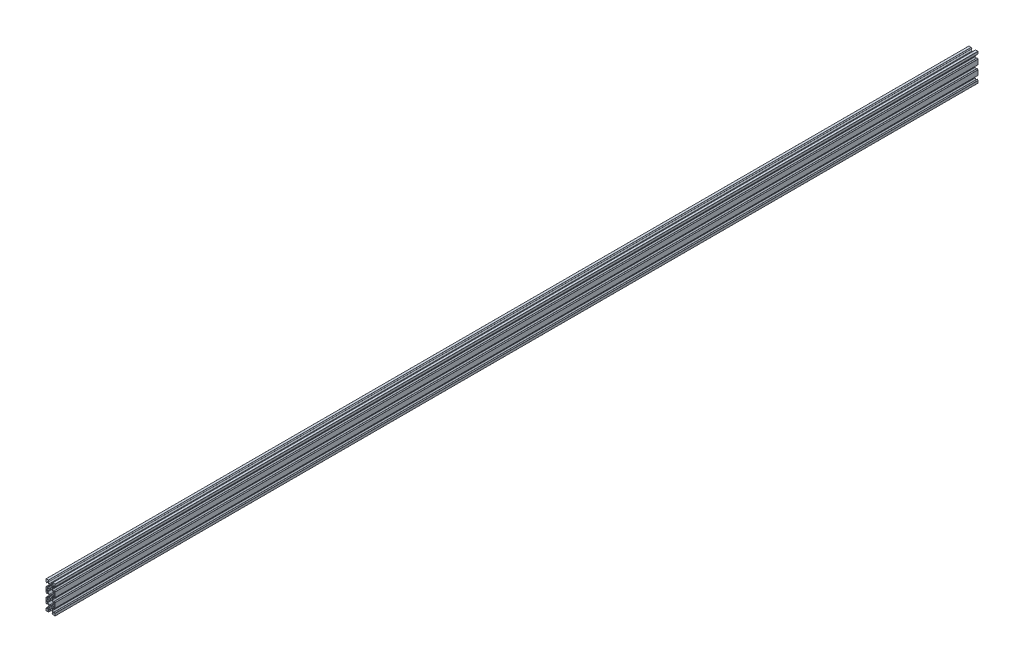
SolidWorks part; units mm, degrees
material "6063-T5"
ref_plane "Plan de face" through (0, 0, 0) normal (0, 0, 1) x (1, 0, 0)
ref_plane "Plan de dessus" through (0, 0, 0) normal (0, 1, 0) x (1, 0, 0)
ref_plane "Plan de droite" through (0, 0, 0) normal (1, 0, 0) x (0, 0, -1)
sketch "Esquisse1" plane through (0, 0, 0) normal (0, 0, 1) x (1, 0, 0)
  line L12 (10.4135, -7.6873) -> (8.8378, -7.6873)
  line L13 (8.6256, -7.5995) -> (5.4414, -4.4152)
  line L14 (5.2292, -4.3273) -> (3.0331, -4.3273)
  line L15 (3.0331, -4.3273) -> (2.5135, -4.0273)
  line L16 (2.5135, -4.0273) -> (1.9939, -4.3273)
  line L17 (1.9939, -4.3273) -> (-0.2022, -4.3273)
  line L18 (-0.4144, -4.4152) -> (-3.5986, -7.5995)
  line L19 (-3.8108, -7.6873) -> (-5.3865, -7.6873)
  line L20 (-5.6865, -7.9873) -> (-5.6865, -10.4267)
  line L21 (-5.6865, -10.4267) -> (-5.6865, -12.866)
  line L22 (-5.3865, -13.166) -> (-3.8108, -13.166)
  line L23 (-3.5986, -13.2539) -> (-0.4144, -16.4382)
  line L24 (-0.2022, -16.526) -> (1.9939, -16.526)
  line L25 (1.9939, -16.526) -> (2.5135, -16.826)
  line L26 (2.5135, -16.826) -> (3.0331, -16.526)
  line L27 (3.0331, -16.526) -> (5.2292, -16.526)
  line L28 (5.4414, -16.4382) -> (8.6256, -13.2539)
  line L29 (8.8378, -13.166) -> (10.4135, -13.166)
  line L30 (10.7135, -12.866) -> (10.7135, -10.4267)
  line L31 (10.7135, -10.4267) -> (10.7135, -7.9873)
  line L38 (10.4135, 12.3127) -> (8.8378, 12.3127)
  line L39 (8.6256, 12.4005) -> (5.4414, 15.5848)
  line L40 (5.2292, 15.6727) -> (3.0331, 15.6727)
  line L41 (3.0331, 15.6727) -> (2.5135, 15.9727)
  line L42 (2.5135, 15.9727) -> (1.9939, 15.6727)
  line L43 (1.9939, 15.6727) -> (-0.2022, 15.6727)
  line L44 (-0.4144, 15.5848) -> (-3.5986, 12.4005)
  line L45 (-3.8108, 12.3127) -> (-5.3865, 12.3127)
  line L46 (-5.6865, 12.0127) -> (-5.6865, 9.5733)
  line L47 (-5.6865, 9.5733) -> (-5.6865, 7.134)
  line L48 (-5.3865, 6.834) -> (-3.8108, 6.834)
  line L49 (-3.5986, 6.7461) -> (-0.4144, 3.5618)
  line L50 (-0.2022, 3.474) -> (1.9939, 3.474)
  line L51 (1.9939, 3.474) -> (2.5135, 3.174)
  line L52 (2.5135, 3.174) -> (3.0331, 3.474)
  line L53 (3.0331, 3.474) -> (5.2292, 3.474)
  line L54 (5.4414, 3.5618) -> (8.6256, 6.7461)
  line L55 (8.8378, 6.834) -> (10.4135, 6.834)
  line L56 (10.7135, 7.134) -> (10.7135, 9.5733)
  line L57 (10.7135, 9.5733) -> (10.7135, 12.0127)
  line L64 (6.1142, 19.5733) -> (6.4142, 20.0929)
  line L65 (6.4142, 20.0929) -> (6.4142, 22.2891)
  line L66 (6.502, 22.5012) -> (8.9856, 24.9848)
  line L67 (9.1978, 25.0727) -> (10.4135, 25.0727)
  line L68 (10.7135, 24.7727) -> (10.7135, 22.7733)
  line L69 (10.8842, 22.7026) -> (12.4256, 24.244)
  line L70 (12.5135, 24.4562) -> (12.5135, 29.2733)
  line L71 (12.2135, 29.5733) -> (7.3963, 29.5733)
  line L72 (7.1842, 29.4855) -> (5.6428, 27.944)
  line L73 (5.7135, 27.7733) -> (7.7128, 27.7733)
  line L74 (8.0128, 27.4733) -> (8.0128, 26.2576)
  line L75 (7.925, 26.0455) -> (5.4414, 23.5618)
  line L78 (5.2292, 23.474) -> (3.0331, 23.474)
  line L79 (3.0331, 23.474) -> (2.5135, 23.174)
  line L80 (2.5135, 23.174) -> (1.9939, 23.474)
  line L81 (1.9939, 23.474) -> (-0.2022, 23.474)
  line L84 (-0.4144, 23.5618) -> (-2.898, 26.0455)
  line L85 (-2.9858, 26.2576) -> (-2.9858, 27.4733)
  line L86 (-2.6858, 27.7733) -> (-0.6865, 27.7733)
  line L87 (-0.6158, 27.944) -> (-2.1572, 29.4855)
  line L88 (-2.3693, 29.5733) -> (-7.1865, 29.5733)
  line L89 (-7.4865, 29.2733) -> (-7.4865, 24.4562)
  line L90 (-7.3986, 24.244) -> (-5.8572, 22.7026)
  line L91 (-5.6865, 22.7733) -> (-5.6865, 24.7727)
  line L92 (-5.3865, 25.0727) -> (-4.1708, 25.0727)
  line L95 (-3.9586, 24.9848) -> (-1.475, 22.5012)
  line L96 (-1.3872, 22.2891) -> (-1.3872, 20.0929)
  line L97 (-1.3872, 20.0929) -> (-1.0872, 19.5733)
  line L98 (-1.0872, 19.5733) -> (-1.3872, 19.0537)
  line L99 (-1.3872, 19.0537) -> (-1.3872, 16.8576)
  line L100 (-1.475, 16.6455) -> (-3.9586, 14.1618)
  line L101 (-4.1708, 14.074) -> (-5.3865, 14.074)
  line L102 (-5.6865, 14.374) -> (-5.6865, 16.3733)
  line L103 (-5.8572, 16.444) -> (-7.3986, 14.9026)
  line L104 (-7.4865, 14.6905) -> (-7.4865, 9.5733)
  line L105 (-7.4865, 9.5733) -> (-7.4865, 4.4562)
  line L106 (-7.3986, 4.244) -> (-5.8572, 2.7026)
  line L107 (-5.6865, 2.7733) -> (-5.6865, 4.7727)
  line L108 (-5.3865, 5.0727) -> (-4.1708, 5.0727)
  line L109 (-3.9586, 4.9848) -> (-1.475, 2.5012)
  line L110 (-1.3872, 2.2891) -> (-1.3872, 0.0929)
  line L111 (-1.3872, 0.0929) -> (-1.0872, -0.4267)
  line L112 (-1.0872, -0.4267) -> (-1.3872, -0.9463)
  line L113 (-1.3872, -0.9463) -> (-1.3872, -3.1424)
  line L114 (-1.475, -3.3545) -> (-3.9586, -5.8382)
  line L115 (-4.1708, -5.926) -> (-5.3865, -5.926)
  line L116 (-5.6865, -5.626) -> (-5.6865, -3.6267)
  line L117 (-5.8572, -3.556) -> (-7.3986, -5.0974)
  line L118 (-7.4865, -5.3095) -> (-7.4865, -10.4267)
  line L119 (-7.4865, -10.4267) -> (-7.4865, -15.5438)
  line L120 (-7.3986, -15.756) -> (-5.8572, -17.2974)
  line L121 (-5.6865, -17.2267) -> (-5.6865, -15.2273)
  line L122 (-5.3865, -14.9273) -> (-4.1708, -14.9273)
  line L123 (-3.9586, -15.0152) -> (-1.475, -17.4988)
  line L124 (-1.3872, -17.7109) -> (-1.3872, -19.9071)
  line L125 (-1.3872, -19.9071) -> (-1.0872, -20.4267)
  line L126 (-1.0872, -20.4267) -> (-1.3872, -20.9463)
  line L127 (-1.3872, -20.9463) -> (-1.3872, -23.1424)
  line L128 (-1.475, -23.3545) -> (-3.9586, -25.8382)
  line L131 (-4.1708, -25.926) -> (-5.3865, -25.926)
  line L132 (-5.6865, -25.626) -> (-5.6865, -23.6267)
  line L133 (-5.8572, -23.556) -> (-7.3986, -25.0974)
  line L134 (-7.4865, -25.3095) -> (-7.4865, -30.1267)
  line L135 (-7.1865, -30.4267) -> (-2.3693, -30.4267)
  line L136 (-2.1572, -30.3388) -> (-0.6158, -28.7974)
  line L137 (-0.6865, -28.6267) -> (-2.6858, -28.6267)
  line L138 (-2.9858, -28.3267) -> (-2.9858, -27.1109)
  line L139 (-2.898, -26.8988) -> (-0.4144, -24.4152)
  line L142 (-0.2022, -24.3273) -> (1.9939, -24.3273)
  line L143 (1.9939, -24.3273) -> (2.5135, -24.0273)
  line L144 (2.5135, -24.0273) -> (3.0331, -24.3273)
  line L145 (3.0331, -24.3273) -> (5.2292, -24.3273)
  line L148 (5.4414, -24.4152) -> (7.925, -26.8988)
  line L149 (8.0128, -27.1109) -> (8.0128, -28.3267)
  line L150 (7.7128, -28.6267) -> (5.7135, -28.6267)
  line L151 (5.6428, -28.7974) -> (7.1842, -30.3388)
  line L152 (7.3963, -30.4267) -> (12.2135, -30.4267)
  line L153 (12.5135, -30.1267) -> (12.5135, -25.3095)
  line L154 (12.4256, -25.0974) -> (10.8842, -23.556)
  line L155 (10.7135, -23.6267) -> (10.7135, -25.626)
  line L156 (10.4135, -25.926) -> (9.1978, -25.926)
  line L157 (8.9856, -25.8382) -> (6.502, -23.3545)
  line L158 (6.4142, -23.1424) -> (6.4142, -20.9463)
  line L159 (6.4142, -20.9463) -> (6.1142, -20.4267)
  line L160 (6.1142, -20.4267) -> (6.4142, -19.9071)
  line L161 (6.4142, -19.9071) -> (6.4142, -17.7109)
  line L162 (6.502, -17.4988) -> (8.9856, -15.0152)
  line L163 (9.1978, -14.9273) -> (10.4135, -14.9273)
  line L164 (10.7135, -15.2273) -> (10.7135, -17.2267)
  line L165 (10.8842, -17.2974) -> (12.4256, -15.756)
  line L166 (12.5135, -15.5438) -> (12.5135, -10.4267)
  line L167 (12.5135, -10.4267) -> (12.5135, -5.3095)
  line L168 (12.4256, -5.0974) -> (10.8842, -3.556)
  line L169 (10.7135, -3.6267) -> (10.7135, -5.626)
  line L170 (10.4135, -5.926) -> (9.1978, -5.926)
  line L171 (8.9856, -5.8382) -> (6.502, -3.3545)
  line L172 (6.4142, -3.1424) -> (6.4142, -0.9463)
  line L173 (6.4142, -0.9463) -> (6.1142, -0.4267)
  line L174 (6.1142, -0.4267) -> (6.4142, 0.0929)
  line L175 (6.4142, 0.0929) -> (6.4142, 2.2891)
  line L176 (6.502, 2.5012) -> (8.9856, 4.9848)
  line L177 (9.1978, 5.0727) -> (10.4135, 5.0727)
  line L178 (10.7135, 4.7727) -> (10.7135, 2.7733)
  line L179 (10.8842, 2.7026) -> (12.4256, 4.244)
  line L180 (12.5135, 4.4562) -> (12.5135, 9.5733)
  line L181 (12.5135, 9.5733) -> (12.5135, 14.6905)
  line L182 (12.4256, 14.9026) -> (10.8842, 16.444)
  line L183 (10.7135, 16.3733) -> (10.7135, 14.374)
  line L184 (10.4135, 14.074) -> (9.1978, 14.074)
  line L185 (8.9856, 14.1618) -> (6.502, 16.6455)
  line L186 (6.4142, 16.8576) -> (6.4142, 19.0537)
  line L187 (6.4142, 19.0537) -> (6.1142, 19.5733)
  arc A0 (0.4135, -20.4267) -> (2.5135, -22.5267) centre (2.5135, -20.4267) ccw
  arc A1 (2.5135, -22.5267) -> (4.6135, -20.4267) centre (2.5135, -20.4267) ccw
  arc A2 (4.6135, -20.4267) -> (2.5135, -18.3267) centre (2.5135, -20.4267) ccw
  arc A3 (2.5135, -18.3267) -> (0.4135, -20.4267) centre (2.5135, -20.4267) ccw
  arc A4 (-0.2022, -24.3273) -> (-0.4144, -24.4152) centre (-0.2022, -24.6273) ccw
  arc A5 (5.4414, -24.4152) -> (5.2292, -24.3273) centre (5.2292, -24.6273) ccw
  arc A6 (-4.1708, -25.926) -> (-3.9586, -25.8382) centre (-4.1708, -25.626) ccw
  arc A7 (10.7135, -7.9873) -> (10.4135, -7.6873) centre (10.4135, -7.9873) ccw
  arc A8 (8.6256, -7.5995) -> (8.8378, -7.6873) centre (8.8378, -7.3873) ccw
  arc A9 (5.4414, -4.4152) -> (5.2292, -4.3273) centre (5.2292, -4.6273) ccw
  arc A10 (-0.2022, -4.3273) -> (-0.4144, -4.4152) centre (-0.2022, -4.6273) ccw
  arc A11 (-3.8108, -7.6873) -> (-3.5986, -7.5995) centre (-3.8108, -7.3873) ccw
  arc A12 (-5.3865, -7.6873) -> (-5.6865, -7.9873) centre (-5.3865, -7.9873) ccw
  arc A13 (-5.6865, -12.866) -> (-5.3865, -13.166) centre (-5.3865, -12.866) ccw
  arc A14 (-3.5986, -13.2539) -> (-3.8108, -13.166) centre (-3.8108, -13.466) ccw
  arc A15 (-0.4144, -16.4382) -> (-0.2022, -16.526) centre (-0.2022, -16.226) ccw
  arc A16 (5.2292, -16.526) -> (5.4414, -16.4382) centre (5.2292, -16.226) ccw
  arc A17 (8.8378, -13.166) -> (8.6256, -13.2539) centre (8.8378, -13.466) ccw
  arc A18 (10.4135, -13.166) -> (10.7135, -12.866) centre (10.4135, -12.866) ccw
  arc A19 (0.4135, -0.4267) -> (2.5135, -2.5267) centre (2.5135, -0.4267) ccw
  arc A20 (2.5135, -2.5267) -> (4.6135, -0.4267) centre (2.5135, -0.4267) ccw
  arc A21 (4.6135, -0.4267) -> (2.5135, 1.6733) centre (2.5135, -0.4267) ccw
  arc A22 (2.5135, 1.6733) -> (0.4135, -0.4267) centre (2.5135, -0.4267) ccw
  arc A23 (10.7135, 12.0127) -> (10.4135, 12.3127) centre (10.4135, 12.0127) ccw
  arc A24 (8.6256, 12.4005) -> (8.8378, 12.3127) centre (8.8378, 12.6127) ccw
  arc A25 (5.4414, 15.5848) -> (5.2292, 15.6727) centre (5.2292, 15.3727) ccw
  arc A26 (-0.2022, 15.6727) -> (-0.4144, 15.5848) centre (-0.2022, 15.3727) ccw
  arc A27 (-3.8108, 12.3127) -> (-3.5986, 12.4005) centre (-3.8108, 12.6127) ccw
  arc A28 (-5.3865, 12.3127) -> (-5.6865, 12.0127) centre (-5.3865, 12.0127) ccw
  arc A29 (-5.6865, 7.134) -> (-5.3865, 6.834) centre (-5.3865, 7.134) ccw
  arc A30 (-3.5986, 6.7461) -> (-3.8108, 6.834) centre (-3.8108, 6.534) ccw
  arc A31 (-0.4144, 3.5618) -> (-0.2022, 3.474) centre (-0.2022, 3.774) ccw
  arc A32 (5.2292, 3.474) -> (5.4414, 3.5618) centre (5.2292, 3.774) ccw
  arc A33 (8.8378, 6.834) -> (8.6256, 6.7461) centre (8.8378, 6.534) ccw
  arc A34 (10.4135, 6.834) -> (10.7135, 7.134) centre (10.4135, 7.134) ccw
  arc A35 (-0.4144, 23.5618) -> (-0.2022, 23.474) centre (-0.2022, 23.774) ccw
  arc A36 (5.2292, 23.474) -> (5.4414, 23.5618) centre (5.2292, 23.774) ccw
  arc A37 (-3.9586, 24.9848) -> (-4.1708, 25.0727) centre (-4.1708, 24.7727) ccw
  arc A38 (0.4135, 19.5733) -> (2.5135, 17.4733) centre (2.5135, 19.5733) ccw
  arc A39 (2.5135, 17.4733) -> (4.6135, 19.5733) centre (2.5135, 19.5733) ccw
  arc A40 (4.6135, 19.5733) -> (2.5135, 21.6733) centre (2.5135, 19.5733) ccw
  arc A41 (2.5135, 21.6733) -> (0.4135, 19.5733) centre (2.5135, 19.5733) ccw
  arc A42 (6.502, 22.5012) -> (6.4142, 22.2891) centre (6.7142, 22.2891) ccw
  arc A43 (9.1978, 25.0727) -> (8.9856, 24.9848) centre (9.1978, 24.7727) ccw
  arc A44 (10.7135, 24.7727) -> (10.4135, 25.0727) centre (10.4135, 24.7727) ccw
  arc A45 (10.7135, 22.7733) -> (10.8842, 22.7026) centre (10.8135, 22.7733) ccw
  arc A46 (12.4256, 24.244) -> (12.5135, 24.4562) centre (12.2135, 24.4562) ccw
  arc A47 (12.5135, 29.2733) -> (12.2135, 29.5733) centre (12.2135, 29.2733) ccw
  arc A48 (7.3963, 29.5733) -> (7.1842, 29.4855) centre (7.3963, 29.2733) ccw
  arc A49 (5.6428, 27.944) -> (5.7135, 27.7733) centre (5.7135, 27.8733) ccw
  arc A50 (8.0128, 27.4733) -> (7.7128, 27.7733) centre (7.7128, 27.4733) ccw
  arc A51 (7.925, 26.0455) -> (8.0128, 26.2576) centre (7.7128, 26.2576) ccw
  arc A52 (-2.9858, 26.2576) -> (-2.898, 26.0455) centre (-2.6858, 26.2576) ccw
  arc A53 (-2.6858, 27.7733) -> (-2.9858, 27.4733) centre (-2.6858, 27.4733) ccw
  arc A54 (-0.6865, 27.7733) -> (-0.6158, 27.944) centre (-0.6865, 27.8733) ccw
  arc A55 (-2.1572, 29.4855) -> (-2.3693, 29.5733) centre (-2.3693, 29.2733) ccw
  arc A56 (-7.1865, 29.5733) -> (-7.4865, 29.2733) centre (-7.1865, 29.2733) ccw
  arc A57 (-7.4865, 24.4562) -> (-7.3986, 24.244) centre (-7.1865, 24.4562) ccw
  arc A58 (-5.8572, 22.7026) -> (-5.6865, 22.7733) centre (-5.7865, 22.7733) ccw
  arc A59 (-5.3865, 25.0727) -> (-5.6865, 24.7727) centre (-5.3865, 24.7727) ccw
  arc A60 (-1.3872, 22.2891) -> (-1.475, 22.5012) centre (-1.6872, 22.2891) ccw
  arc A61 (-1.475, 16.6455) -> (-1.3872, 16.8576) centre (-1.6872, 16.8576) ccw
  arc A62 (-4.1708, 14.074) -> (-3.9586, 14.1618) centre (-4.1708, 14.374) ccw
  arc A63 (-5.6865, 14.374) -> (-5.3865, 14.074) centre (-5.3865, 14.374) ccw
  arc A64 (-5.6865, 16.3733) -> (-5.8572, 16.444) centre (-5.7865, 16.3733) ccw
  arc A65 (-7.3986, 14.9026) -> (-7.4865, 14.6905) centre (-7.1865, 14.6905) ccw
  arc A66 (-7.4865, 4.4562) -> (-7.3986, 4.244) centre (-7.1865, 4.4562) ccw
  arc A67 (-5.8572, 2.7026) -> (-5.6865, 2.7733) centre (-5.7865, 2.7733) ccw
  arc A68 (-5.3865, 5.0727) -> (-5.6865, 4.7727) centre (-5.3865, 4.7727) ccw
  arc A69 (-3.9586, 4.9848) -> (-4.1708, 5.0727) centre (-4.1708, 4.7727) ccw
  arc A70 (-1.3872, 2.2891) -> (-1.475, 2.5012) centre (-1.6872, 2.2891) ccw
  arc A71 (-1.475, -3.3545) -> (-1.3872, -3.1424) centre (-1.6872, -3.1424) ccw
  arc A72 (-4.1708, -5.926) -> (-3.9586, -5.8382) centre (-4.1708, -5.626) ccw
  arc A73 (-5.6865, -5.626) -> (-5.3865, -5.926) centre (-5.3865, -5.626) ccw
  arc A74 (-5.6865, -3.6267) -> (-5.8572, -3.556) centre (-5.7865, -3.6267) ccw
  arc A75 (-7.3986, -5.0974) -> (-7.4865, -5.3095) centre (-7.1865, -5.3095) ccw
  arc A76 (-7.4865, -15.5438) -> (-7.3986, -15.756) centre (-7.1865, -15.5438) ccw
  arc A77 (-5.8572, -17.2974) -> (-5.6865, -17.2267) centre (-5.7865, -17.2267) ccw
  arc A78 (-5.3865, -14.9273) -> (-5.6865, -15.2273) centre (-5.3865, -15.2273) ccw
  arc A79 (-3.9586, -15.0152) -> (-4.1708, -14.9273) centre (-4.1708, -15.2273) ccw
  arc A80 (-1.3872, -17.7109) -> (-1.475, -17.4988) centre (-1.6872, -17.7109) ccw
  arc A81 (-1.475, -23.3545) -> (-1.3872, -23.1424) centre (-1.6872, -23.1424) ccw
  arc A82 (-5.6865, -25.626) -> (-5.3865, -25.926) centre (-5.3865, -25.626) ccw
  arc A83 (-5.6865, -23.6267) -> (-5.8572, -23.556) centre (-5.7865, -23.6267) ccw
  arc A84 (-7.3986, -25.0974) -> (-7.4865, -25.3095) centre (-7.1865, -25.3095) ccw
  arc A85 (-7.4865, -30.1267) -> (-7.1865, -30.4267) centre (-7.1865, -30.1267) ccw
  arc A86 (-2.3693, -30.4267) -> (-2.1572, -30.3388) centre (-2.3693, -30.1267) ccw
  arc A87 (-0.6158, -28.7974) -> (-0.6865, -28.6267) centre (-0.6865, -28.7267) ccw
  arc A88 (-2.9858, -28.3267) -> (-2.6858, -28.6267) centre (-2.6858, -28.3267) ccw
  arc A89 (-2.898, -26.8988) -> (-2.9858, -27.1109) centre (-2.6858, -27.1109) ccw
  arc A90 (8.0128, -27.1109) -> (7.925, -26.8988) centre (7.7128, -27.1109) ccw
  arc A91 (7.7128, -28.6267) -> (8.0128, -28.3267) centre (7.7128, -28.3267) ccw
  arc A92 (5.7135, -28.6267) -> (5.6428, -28.7974) centre (5.7135, -28.7267) ccw
  arc A93 (7.1842, -30.3388) -> (7.3963, -30.4267) centre (7.3963, -30.1267) ccw
  arc A94 (12.2135, -30.4267) -> (12.5135, -30.1267) centre (12.2135, -30.1267) ccw
  arc A95 (12.5135, -25.3095) -> (12.4256, -25.0974) centre (12.2135, -25.3095) ccw
  arc A96 (10.8842, -23.556) -> (10.7135, -23.6267) centre (10.8135, -23.6267) ccw
  arc A97 (10.4135, -25.926) -> (10.7135, -25.626) centre (10.4135, -25.626) ccw
  arc A98 (8.9856, -25.8382) -> (9.1978, -25.926) centre (9.1978, -25.626) ccw
  arc A99 (6.4142, -23.1424) -> (6.502, -23.3545) centre (6.7142, -23.1424) ccw
  arc A100 (6.502, -17.4988) -> (6.4142, -17.7109) centre (6.7142, -17.7109) ccw
  arc A101 (9.1978, -14.9273) -> (8.9856, -15.0152) centre (9.1978, -15.2273) ccw
  arc A102 (10.7135, -15.2273) -> (10.4135, -14.9273) centre (10.4135, -15.2273) ccw
  arc A103 (10.7135, -17.2267) -> (10.8842, -17.2974) centre (10.8135, -17.2267) ccw
  arc A104 (12.4256, -15.756) -> (12.5135, -15.5438) centre (12.2135, -15.5438) ccw
  arc A105 (12.5135, -5.3095) -> (12.4256, -5.0974) centre (12.2135, -5.3095) ccw
  arc A106 (10.8842, -3.556) -> (10.7135, -3.6267) centre (10.8135, -3.6267) ccw
  arc A107 (10.4135, -5.926) -> (10.7135, -5.626) centre (10.4135, -5.626) ccw
  arc A108 (8.9856, -5.8382) -> (9.1978, -5.926) centre (9.1978, -5.626) ccw
  arc A109 (6.4142, -3.1424) -> (6.502, -3.3545) centre (6.7142, -3.1424) ccw
  arc A110 (6.502, 2.5012) -> (6.4142, 2.2891) centre (6.7142, 2.2891) ccw
  arc A111 (9.1978, 5.0727) -> (8.9856, 4.9848) centre (9.1978, 4.7727) ccw
  arc A112 (10.7135, 4.7727) -> (10.4135, 5.0727) centre (10.4135, 4.7727) ccw
  arc A113 (10.7135, 2.7733) -> (10.8842, 2.7026) centre (10.8135, 2.7733) ccw
  arc A114 (12.4256, 4.244) -> (12.5135, 4.4562) centre (12.2135, 4.4562) ccw
  arc A115 (12.5135, 14.6905) -> (12.4256, 14.9026) centre (12.2135, 14.6905) ccw
  arc A116 (10.8842, 16.444) -> (10.7135, 16.3733) centre (10.8135, 16.3733) ccw
  arc A117 (10.4135, 14.074) -> (10.7135, 14.374) centre (10.4135, 14.374) ccw
  arc A118 (8.9856, 14.1618) -> (9.1978, 14.074) centre (9.1978, 14.374) ccw
  arc A119 (6.4142, 16.8576) -> (6.502, 16.6455) centre (6.7142, 16.8576) ccw
  dimension "D1" = 60
extrude "Boss.-Extru.1" add sketch "Esquisse1" along normal blind 2000
